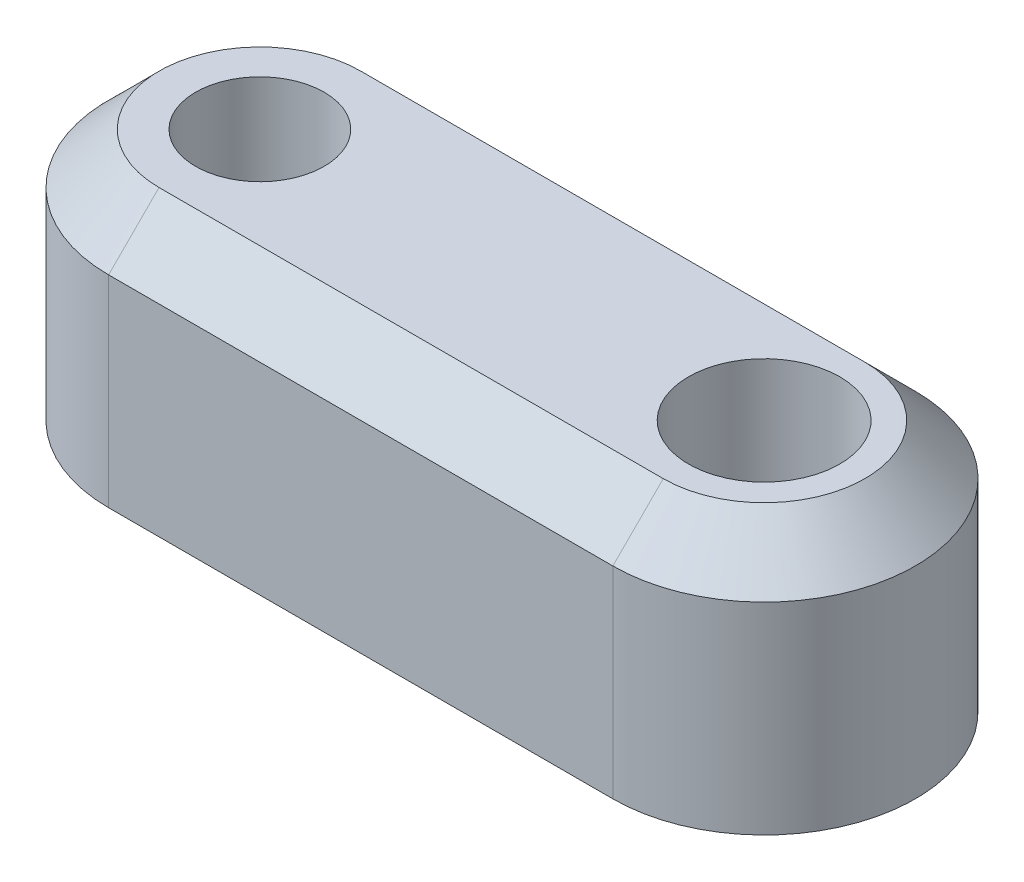
SolidWorks part; units mm, degrees
ref_plane "前视基准面" through (0, 0, 0) normal (0, 0, 1) x (1, 0, 0)
ref_plane "上视基准面" through (0, 0, 0) normal (0, 1, 0) x (1, 0, 0)
ref_plane "右视基准面" through (0, 0, 0) normal (1, 0, 0) x (0, 0, -1)
other "Configuration Table"
sketch "草图1" plane through (0, 0, 0) normal (0, 1, 0) x (1, 0, 0)
  line L0 (0, 0) -> (20, 0) construction
  line L1 (0, 6) -> (20, 6)
  line L2 (0, -6) -> (20, -6)
  arc A0 (0, 6) -> (0, -6) centre (0, 0) ccw
  arc A1 (20, -6) -> (20, 6) centre (20, 0) ccw
  point P3 (10, 0)
  dimension "D1" = 12
  dimension "D2" = 20
extrude "凸台-拉伸1" add sketch "草图1" along normal blind 10
sketch "草图2" plane through (0, 0, 0) normal (0, 0, 1) x (1, 0, 0)
  line L0 (0, 0) -> (0, 10) construction
  line L1 (0, 10) -> (-2.55, 10)
  line L2 (0, 10) -> (-6, 10) construction
  line L3 (-2.55, 10) -> (-2.55, 5)
  line L4 (-2.55, 5) -> (-1.6, 5)
  line L5 (-1.6, 5) -> (-1.6, 2)
  line L6 (-1.6, 2) -> (-2.55, 2)
  line L7 (-2.55, 2) -> (-2.55, 0)
  line L8 (-6, 0) -> (0, 0) construction
  line L9 (-2.55, 0) -> (0, 0)
  line L10 (0, 0) -> (0, 10)
  dimension "D1" = 5.1
  dimension "D2" = 3.2
  dimension "D3" = 5
  dimension "D4" = 3
revolve "切除-旋转1" cut sketch "草图2" angle 360 about L0
sketch "草图4" plane through (0, 0, 0) normal (0, 0, 1) x (1, 0, 0)
  line L0 (20, 0) -> (20, 10) construction
  line L1 (20, 10) -> (17, 10)
  line L2 (0, 10) -> (20, 10) construction
  line L3 (17, 10) -> (17, 5)
  line L4 (17, 5) -> (17.425, 5)
  line L5 (17.425, 5) -> (17.425, 0)
  line L6 (0, 0) -> (20, 0) construction
  line L7 (17.425, 0) -> (20, 0)
  line L8 (20, 0) -> (20, 10)
  dimension "D1" = 6
  dimension "D2" = 5.15
  dimension "D3" = 5
revolve "切除-旋转2" cut sketch "草图4" angle 360 about L0
chamfer "倒角1" distance 2 angle 45 4 edges at (10, 10, 6) (26, 10, 0) (-6, 10, 0) (10, 10, -6)
